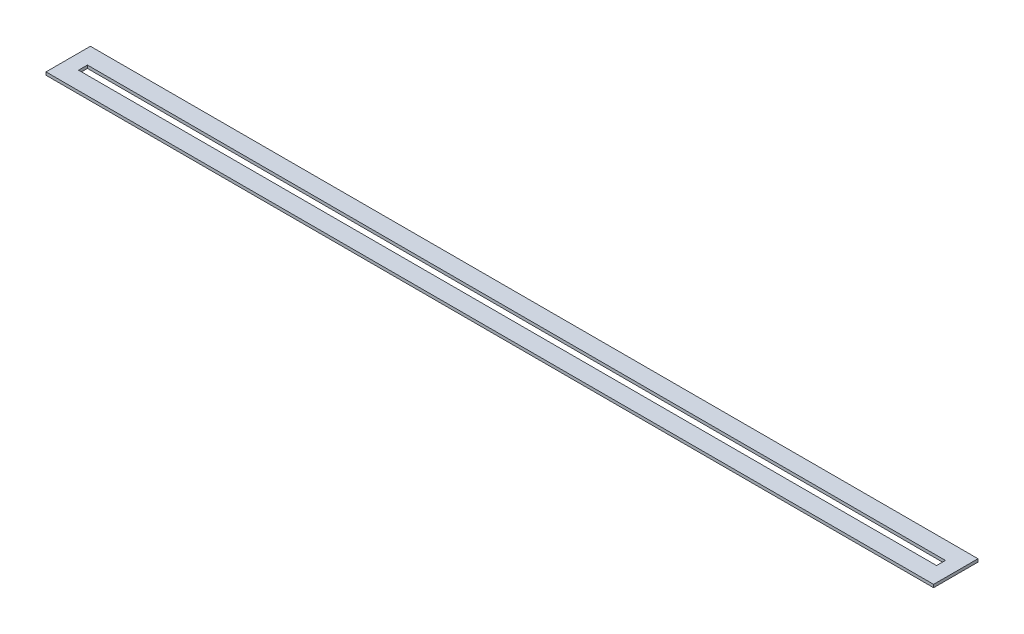
SolidWorks part; units mm, degrees
ref_plane "Front Plane" through (0, 0, 0) normal (0, 0, 1) x (1, 0, 0)
ref_plane "Top Plane" through (0, 0, 0) normal (0, 1, 0) x (1, 0, 0)
ref_plane "Right Plane" through (0, 0, 0) normal (1, 0, 0) x (0, 0, -1)
sketch "Sketch1" plane through (0, 0, 0) normal (0, 1, 0) x (1, 0, 0)
  line L0 (10, -12) -> (590, -12)
  line L1 (0, 0) -> (600, 0)
  line L2 (0, 0) -> (0, -30)
  line L3 (0, -30) -> (600, -30)
  line L4 (600, 0) -> (600, -30)
  line L5 (10, -18) -> (590, -18)
  line L6 (10, -12) -> (10, -18)
  line L7 (590, -12) -> (590, -18)
  line L9 (590, 0) -> (590, -30) construction
  line L10 (0, -12) -> (600, -12) construction
  line L11 (0, -18) -> (600, -18) construction
  line L12 (10, 0) -> (10, -30) construction
extrude "Boss-Extrude1" add sketch "Sketch1" along normal blind 2
